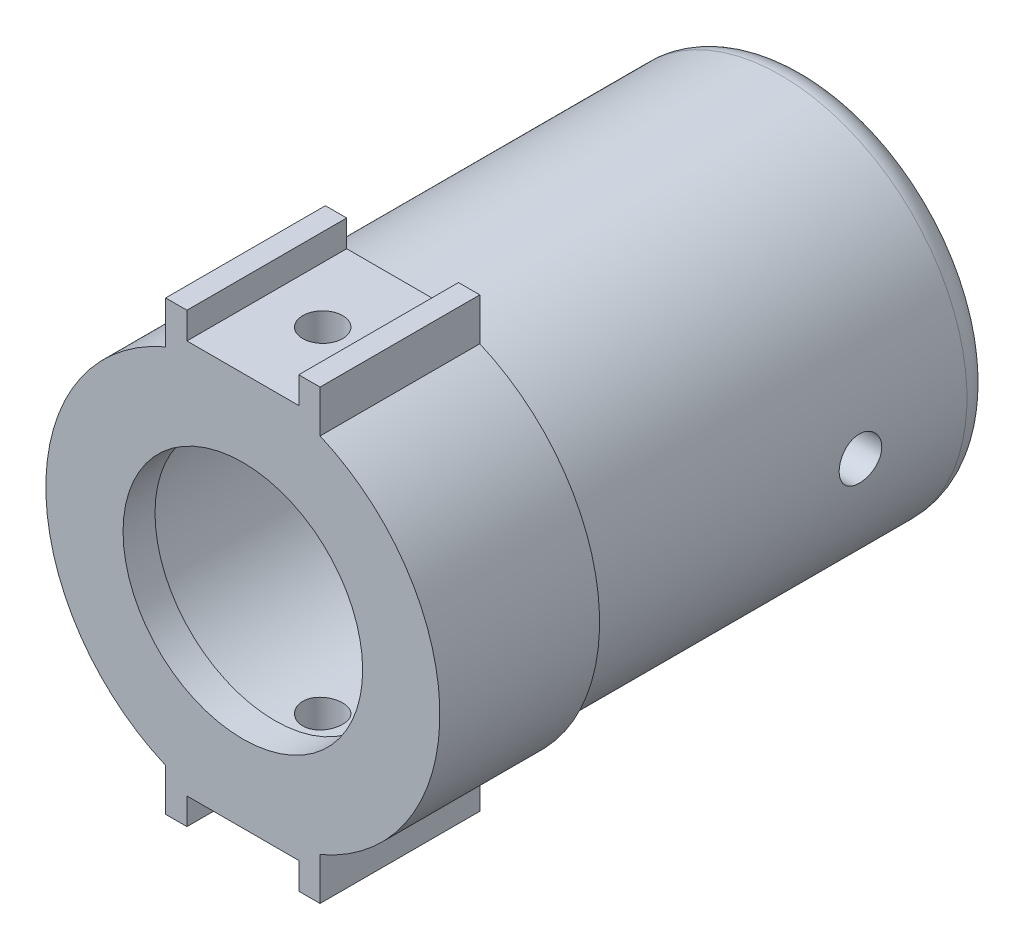
SolidWorks part; units mm, degrees
ref_plane "Front Plane" through (0, 0, 0) normal (0, 0, 1) x (1, 0, 0)
ref_plane "Top Plane" through (0, 0, 0) normal (0, 1, 0) x (1, 0, 0)
ref_plane "Right Plane" through (0, 0, 0) normal (1, 0, 0) x (0, 0, -1)
sketch "Sketch10" plane through (0, 0, 0) normal (0, 0, 1) x (1, 0, 0)
  circle A0 centre (0, 0) radius 4.5
  circle A1 centre (0, 0) radius 7.4
  dimension "D1" = 9
  dimension "D2" = 14.8
extrude "Boss-Extrude3" add sketch "Sketch10" along normal blind 1.2
sketch "Sketch11" plane through (0, 0, 0) normal (0, 0, -1) x (-1, 0, 0)
  circle A0 centre (0, 0) radius 5.2
  circle A1 centre (0, 0) radius 7.4
  circle A2 centre (0, 0) radius 7.4
  dimension "D2" = 10.4
  dimension "D1" = 0
extrude "Boss-Extrude4" add sketch "Sketch11" along normal blind 20
sketch "Sketch13" plane through (0, 0, 1.2) normal (0, 0, 1) x (1, 0, 0)
  line L1 (2.9, 6.4) -> (-2.9, 6.4)
  line L2 (2.9, 6.4) -> (2.9, 8.4)
  line L3 (2.9, 8.4) -> (-2.9, 8.4)
  line L4 (-2.9, 6.4) -> (-2.9, 8.4)
  line L5 (2.9, 6.4) -> (-2.9, 8.4) construction
  line L6 (2.9, 8.4) -> (-2.9, 6.4) construction
  line L7 (2.9, -6.4) -> (-2.9, -6.4)
  line L8 (2.9, -6.4) -> (2.9, -8.4)
  line L9 (2.9, -8.4) -> (-2.9, -8.4)
  line L10 (-2.9, -6.4) -> (-2.9, -8.4)
  line L11 (2.9, -6.4) -> (-2.9, -8.4) construction
  line L12 (2.9, -8.4) -> (-2.9, -6.4) construction
  circle A1 centre (0, 0) radius 7.4
  circle A2 centre (0, 0) radius 7.4
  point P0 (0, 7.4)
  point P8 (0, -7.4)
  circle M6 centre (0, 0) radius 7.4
  dimension "D2" = 5.8
  dimension "D3" = 2
  dimension "D4" = 5.8
  dimension "D5" = 2
  dimension "D1" = 0
extrude "Boss-Extrude5" add sketch "Sketch13" against normal blind 7 contours L4 L2 L3 M6 | L10 L9 L8 M6
sketch "Sketch12" plane through (0, 0, 0) normal (0, 1, 0) x (1, 0, 0)
  line L0 (-7.4, -1.2) -> (7.4, -1.2) construction
  circle A0 centre (0, 1.8) radius 0.75
  dimension "D1" = 1.5
  dimension "D2" = 3
extrude "Cut-Extrude1" cut sketch "Sketch12" against normal blind 11 and the other way blind 10
sketch "Sketch14" plane through (0, 0, 1.2) normal (0, 0, 1) x (1, 0, 0)
  line L1 (-2.1, 8.4) -> (2.1, 8.4)
  line L2 (-2.1, 8.4) -> (-2.1, 7.4)
  line L3 (-2.1, 7.4) -> (2.1, 7.4)
  line L4 (2.1, 8.4) -> (2.1, 7.4)
  line L5 (-2.1, -8.4) -> (2.1, -8.4)
  line L6 (-2.9, -6.8081) -> (-2.9, -8.4)
  line L7 (-2.9, -8.4) -> (2.9, -8.4)
  line L8 (2.9, -8.4) -> (2.9, -6.8081)
  line L9 (2.9, 6.8081) -> (2.9, 8.4)
  line L10 (2.9, 8.4) -> (-2.9, 8.4)
  line L11 (-2.9, 8.4) -> (-2.9, 6.8081)
  line L12 (-2.9, -6.8081) -> (-2.9, -8.4)
  line L13 (-2.9, -8.4) -> (2.9, -8.4)
  line L14 (2.9, -8.4) -> (2.9, -6.8081)
  line L15 (2.9, 6.8081) -> (2.9, 8.4)
  line L16 (2.9, 8.4) -> (-2.9, 8.4)
  line L17 (-2.9, 8.4) -> (-2.9, 6.8081)
  line L18 (-2.1, -8.4) -> (-2.1, -7.4)
  line L19 (-2.1, -7.4) -> (2.1, -7.4)
  line L20 (2.1, -8.4) -> (2.1, -7.4)
  arc A2 (-2.9, 6.8081) -> (-2.9, -6.8081) centre (0, 0) ccw
  arc A3 (2.9, -6.8081) -> (2.9, 6.8081) centre (0, 0) ccw
  arc A4 (-2.9, 6.8081) -> (-2.9, -6.8081) centre (0, 0) ccw
  arc A5 (2.9, -6.8081) -> (2.9, 6.8081) centre (0, 0) ccw
  line M17 (-2.9, -8.4) -> (2.9, -8.4)
  line M21 (2.9, 8.4) -> (-2.9, 8.4)
  dimension "D2" = 1
  dimension "D3" = 1
  dimension "D4" = 4.2
  dimension "D5" = 0.8
  dimension "D6" = 4.2
  dimension "D7" = 0.8
  dimension "D1" = 0
extrude "Cut-Extrude2" cut sketch "Sketch14" against normal blind 6 contours L4 L2 L3 M21 | L20 L19 L18 M17
sketch "Sketch15" plane through (0, 8.4, 0) normal (0, 1, 0) x (1, 0, 0)
  line L0 (-2.9, 4.8) -> (2.9, 4.8)
  line L8 (-2.1, 4.8) -> (2.1, 4.8)
  line L9 (2.1, 4.8) -> (2.1, -1.2)
  line L10 (2.1, -1.2) -> (2.9, -1.2)
  line L11 (2.9, -1.2) -> (2.9, 5.8)
  line L12 (2.9, 5.8) -> (-2.9, 5.8)
  line L13 (-2.9, 5.8) -> (-2.9, -1.2)
  line L14 (-2.9, -1.2) -> (-2.1, -1.2)
  line L15 (-2.1, -1.2) -> (-2.1, 4.8)
  line L16 (-2.1, 4.8) -> (2.1, 4.8)
  line L17 (2.1, 4.8) -> (2.1, -1.2)
  line L18 (2.1, -1.2) -> (2.9, -1.2)
  line L19 (2.9, -1.2) -> (2.9, 5.8)
  line L20 (2.9, 5.8) -> (-2.9, 5.8)
  line L21 (-2.9, 5.8) -> (-2.9, -1.2)
  line L22 (-2.9, -1.2) -> (-2.1, -1.2)
  line L23 (-2.1, -1.2) -> (-2.1, 4.8)
  line M13 (2.9, -1.2) -> (2.9, 5.8)
  line M14 (2.9, 5.8) -> (-2.9, 5.8)
  line M15 (-2.9, 5.8) -> (-2.9, -1.2)
  dimension "D2" = 1
  dimension "D1" = 0
extrude "Cut-Extrude3" cut sketch "Sketch15" against normal up to surface (1.5919 mm away) contours L0 M15 M13 M14
sketch "Sketch18" plane through (0, 0, -5.8) normal (0, 0, -1) x (-1, 0, 0)
  line L3 (-2.9, -6.8081) -> (-2.9, -8.4)
  line L4 (-2.9, -8.4) -> (2.9, -8.4)
  line L5 (2.9, -8.4) -> (2.9, -6.8081)
  line L6 (-2.9, -6.8081) -> (-2.9, -8.4)
  line L7 (-2.9, -8.4) -> (2.9, -8.4)
  line L8 (2.9, -8.4) -> (2.9, -6.8081)
  arc A1 (-2.9, -6.8081) -> (2.9, -6.8081) centre (0, 0) ccw
  arc A2 (-2.9, -6.8081) -> (2.9, -6.8081) centre (0, 0) ccw
  dimension "D1" = 0
extrude "Cut-Extrude6" cut sketch "Sketch18" against normal blind 1
sketch "Sketch16" plane through (0, 0, 0) normal (1, 0, 0) x (0, 0, -1)
  line L0 (0, 0) -> (15, 0) construction
  line L1 (20, -7.4) -> (20, 7.4) construction
  circle A0 centre (15, 0) radius 0.8
  dimension "D1" = 1.6
  dimension "D2" = 5
extrude "Cut-Extrude4" cut sketch "Sketch16" against normal blind 10 and the other way blind 10
sketch "Sketch19" plane through (0, 0, -20) normal (0, 0, -1) x (-1, 0, 0)
  circle A0 centre (0, 0) radius 7
  circle A1 centre (0, 0) radius 7.4
  circle A2 centre (0, 0) radius 7.4
  dimension "D2" = 14
  dimension "D1" = 0
extrude "Cut-Extrude7" cut sketch "Sketch19" against normal up to surface (15.2 mm away) up to face at (2.006, -7.7109, -4.8)
fillet "Fillet1" radius 1 1 edges at (-7, 0, -20)
